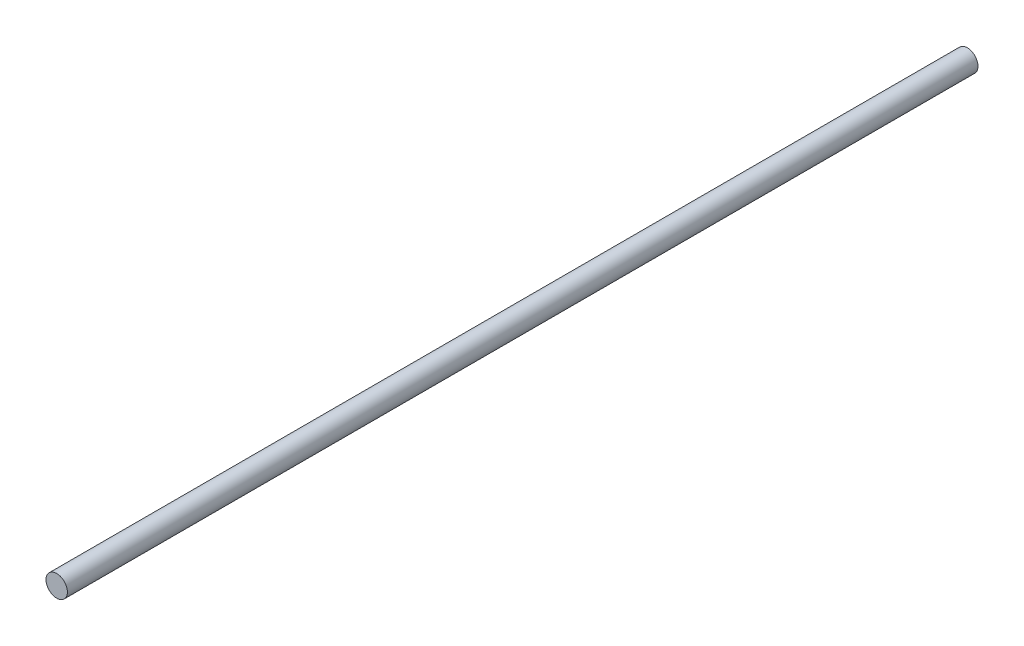
SolidWorks part; units mm, degrees
material "AISI 1010 Steel, hot rolled bar"
ref_plane "Front Plane" through (0, 0, 0) normal (0, 0, 1) x (1, 0, 0)
ref_plane "Top Plane" through (0, 0, 0) normal (0, 1, 0) x (1, 0, 0)
ref_plane "Right Plane" through (0, 0, 0) normal (1, 0, 0) x (0, 0, -1)
sketch "Sketch1" plane through (0, 0, 0) normal (0, 0, 1) x (1, 0, 0)
  circle A0 centre (0, 0) radius 5
  dimension "D1" = 10
extrude "Boss-Extrude1" add sketch "Sketch1" along normal mid plane 425
